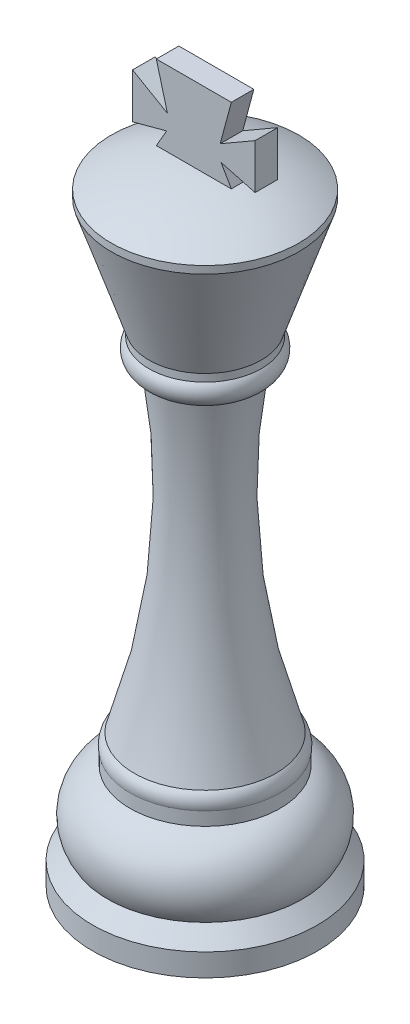
SolidWorks part; units mm, degrees
ref_plane "Front Plane" through (0, 0, 0) normal (0, 0, 1) x (1, 0, 0)
ref_plane "Top Plane" through (0, 0, 0) normal (0, 1, 0) x (1, 0, 0)
ref_plane "Right Plane" through (0, 0, 0) normal (1, 0, 0) x (0, 0, -1)
sketch "Sketch2" plane through (0, 0, 0) normal (0, 0, 1) x (1, 0, 0)
  line L0 (0, -79.693) -> (0, 83.77) construction
  line L1 (0, 0) -> (-15, 0)
  line L2 (-15, 0) -> (-15, 3)
  line L3 (-10, 13.97) -> (-10, 15.75)
  line L4 (0, 0) -> (0, 83.77)
  line L5 (-15, 3) -> (-13, 5)
  line L12 (-7.5, 63.5) -> (-7.5, 64.5)
  line L15 (-12.5, 79.5) -> (-7.5, 64.5)
  line L16 (-12.5, 79.5) -> (-12.5, 80.5)
  arc A0 (-13, 5) -> (-10, 13.97) centre (-7.9981, 8.3138) cw
  arc A1 (-10, 15.75) -> (-9.45, 17.75) centre (-8.0761, 16.2966) cw
  arc A2 (-9.45, 17.75) -> (-6, 60.18) centre (-94.8842, 46.0519) ccw
  arc A3 (-6, 60.18) -> (-7.5, 63.5) centre (-5.9975, 62.18) cw
  arc A4 (-12.5, 80.5) -> (0, 83.77) centre (-0.1378, 58.7704) cw
  dimension "D7" = 6
  dimension "D10" = 2
  dimension "D15" = 90
  dimension "D19" = 2
  dimension "D26" = 25
  dimension "D1" = 15
revolve "Revolve2" add sketch "Sketch2" angle 360 about L0
sketch "Sketch3" plane through (0, 0, 0) normal (0, 0, 1) x (1, 0, 0)
  line L1 (5, 93.77) -> (-5, 93.77)
  line L2 (-5, 93.77) -> (-3.5191, 88.2434)
  line L3 (-3.5191, 88.2434) -> (-8.1714, 90.9293)
  line L4 (-8.1714, 90.9293) -> (-8.1714, 84.9293)
  line L5 (-8.1714, 84.9293) -> (-3.6281, 86.1467)
  line L6 (-3.6281, 86.1467) -> (-5, 83.7704)
  line L7 (-5, 83.7704) -> (0, 83.77)
  line L8 (3.6281, 86.1467) -> (5, 83.7704)
  line L9 (8.1714, 84.9293) -> (3.6281, 86.1467)
  line L10 (8.1714, 90.9293) -> (8.1714, 84.9293)
  line L11 (3.5191, 88.2434) -> (8.1714, 90.9293)
  line L12 (5, 93.77) -> (3.5191, 88.2434)
  line L13 (5, 83.7704) -> (0, 83.77)
  point P4 (-3.648, 88.2088)
  dimension "D3" = 5
  dimension "D4" = 6
  dimension "D5" = 45
  dimension "D7" = 45
extrude "Boss-Extrude1" add sketch "Sketch3" along normal mid plane 3 separate body
